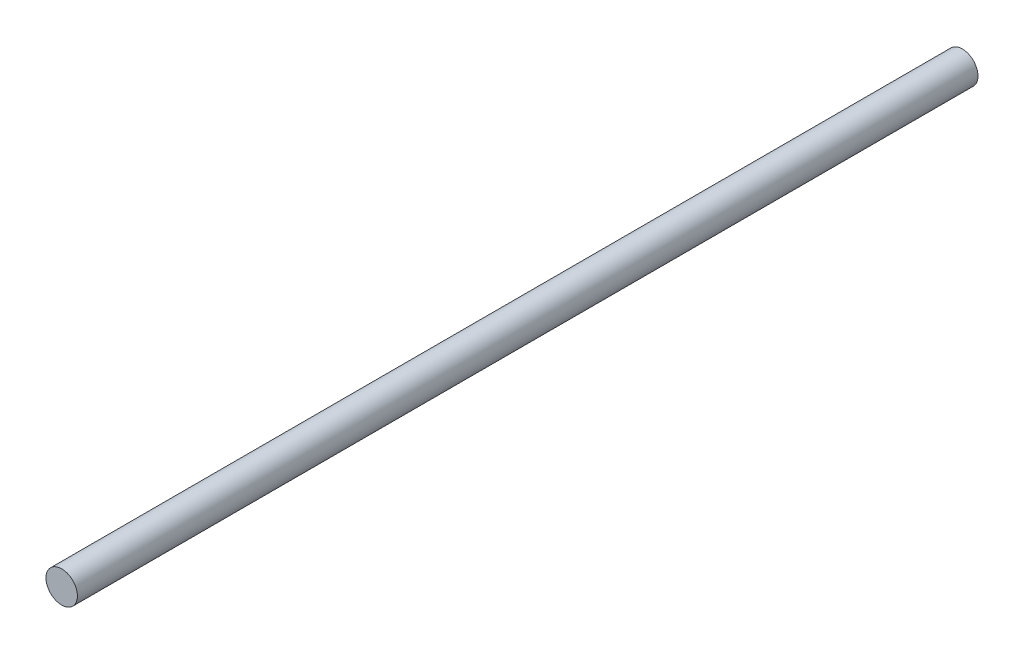
SolidWorks part; units mm, degrees
ref_plane "Front Plane" through (0, 0, 0) normal (0, 0, 1) x (1, 0, 0)
ref_plane "Top Plane" through (0, 0, 0) normal (0, 1, 0) x (1, 0, 0)
ref_plane "Right Plane" through (0, 0, 0) normal (1, 0, 0) x (0, 0, -1)
sketch "Sketch1" plane through (0, 0, 0) normal (0, 0, 1) x (1, 0, 0)
  circle A0 centre (0, 0) radius 3.9878
  dimension "D1" = 7.9756
extrude "Boss-Extrude1" add sketch "Sketch1" along normal blind 228.6 contours A0
